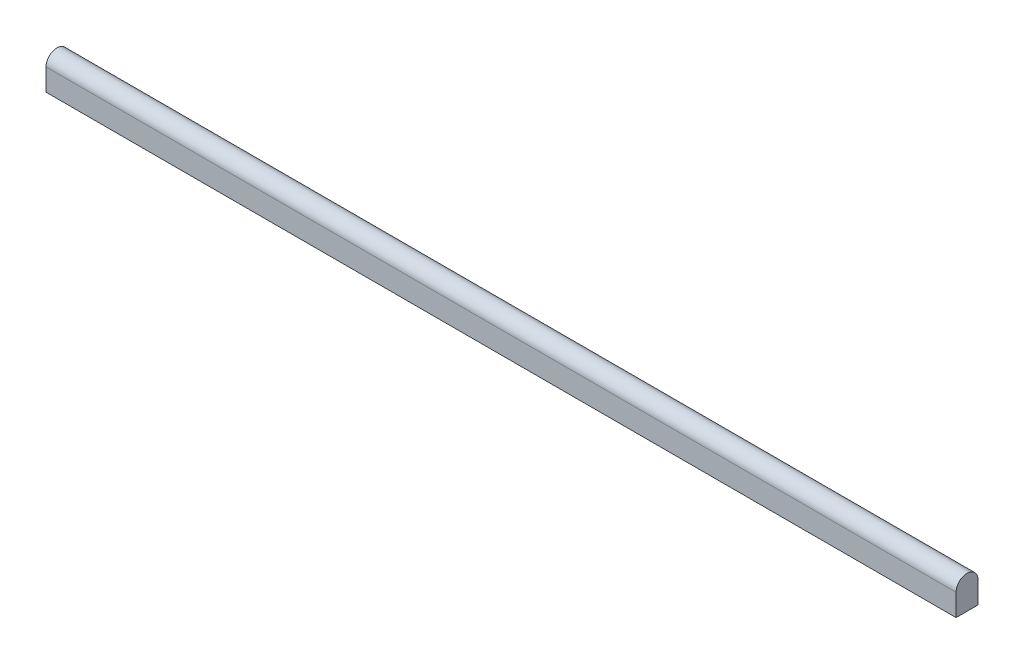
SolidWorks part; units mm, degrees
ref_plane "Plan de face" through (0, 0, 0) normal (0, 0, 1) x (1, 0, 0)
ref_plane "Plan de dessus" through (0, 0, 0) normal (0, 1, 0) x (1, 0, 0)
ref_plane "Plan de droite" through (0, 0, 0) normal (1, 0, 0) x (0, 0, -1)
sketch "Esquisse1" plane through (0, 0, 0) normal (1, 0, 0) x (0, 0, -1)
  line L0 (-2, 0) -> (-2, -4)
  line L1 (-2, -4) -> (2, -4)
  line L2 (2, -4) -> (2, 0)
  arc A0 (-2, 0) -> (2, 0) centre (0, 0) cw
  dimension "D1" = 2
  dimension "D2" = 4
extrude "Extrusion1" add sketch "Esquisse1" along normal blind 166
sketch "Esquisse3" plane through (0, 0, 0) normal (-1, 0, 0) x (0, 0, 1)
  line L6 (-1, 0) -> (-1, -3)
  line L7 (-1, -3) -> (1, -3)
  line L8 (1, -3) -> (1, 0)
  line L9 (-1, 0) -> (-1, -3)
  line L10 (-1, -3) -> (1, -3)
  line L11 (1, -3) -> (1, 0)
  arc A2 (1, 0) -> (-1, 0) centre (0, 0) ccw
  arc A3 (1, 0) -> (-1, 0) centre (0, 0) ccw
  dimension "D1" = 1
extrude "Enlèv. mat.-Extru.2" cut sketch "Esquisse3" against normal blind 10
sketch "Esquisse4" plane through (0, -4, 0) normal (0, -1, 0) x (1, 0, 0)
  line L0 (0, 2) -> (0, -2) construction
  line L1 (0, -0.5) -> (10, -0.5)
  line L2 (0, -0.5) -> (0, 0.5)
  line L3 (0, 0.5) -> (10, 0.5)
  line L4 (10, -0.5) -> (10, 0.5)
  point P6 (0, 0)
  point P7 (0, 0)
  dimension "D1" = 1
  dimension "D2" = 10
extrude "Enlèv. mat.-Extru.3" cut sketch "Esquisse4" against normal blind 2
